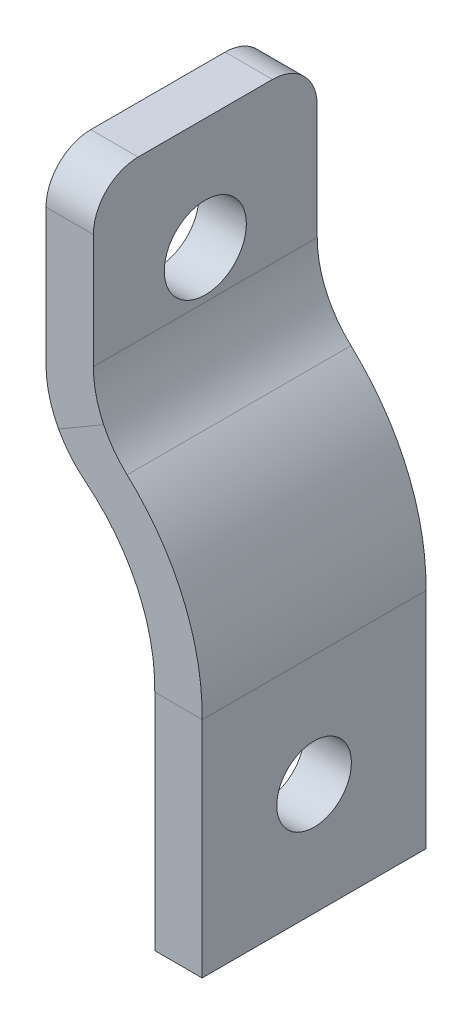
SolidWorks part; units mm, degrees
material "1060 Alloy"
ref_plane "Front Plane" through (0, 0, 0) normal (0, 0, 1) x (1, 0, 0)
ref_plane "Top Plane" through (0, 0, 0) normal (0, 1, 0) x (1, 0, 0)
ref_plane "Right Plane" through (0, 0, 0) normal (1, 0, 0) x (0, 0, -1)
sketch "Sketch1" plane through (0, 0, 0) normal (0, 0, 1) x (1, 0, 0)
  line L0 (-14.2875, 7.5) -> (-14.2875, -7.5)
  line L1 (-7, -20) -> (-7, -35)
  circle A0 centre (0, 0) radius 12.7 construction
  arc A1 (-14.2875, -7.5) -> (-7, -20) centre (-20.9984, -19.7867) cw
  point P3 (-12.7, 0)
  point P4 (0, -12.7)
  dimension "D1" = 25.4
  dimension "D6" = 14
  dimension "D2" = 15
  dimension "D3" = 15
  dimension "D4" = 7
  dimension "D5" = 1.5875
  dimension "D7" = 20
  dimension "D8" = 7.5
sketch "Sketch2" plane through (0, 0, 0) normal (0, 1, 0) x (1, 0, 0)
  line L0 (-14.2875, 0) -> (-6.9984, 0) construction
  line L1 (-12.7, -7.5) -> (-15.875, -7.5)
  line L2 (-12.7, -7.5) -> (-12.7, 7.5)
  line L3 (-12.7, 7.5) -> (-15.875, 7.5)
  line L4 (-15.875, -7.5) -> (-15.875, 7.5)
  line L5 (-12.7, -7.5) -> (-15.875, 7.5) construction
  line L6 (-12.7, 7.5) -> (-15.875, -7.5) construction
  point P0 (-14.2875, 0)
  dimension "D1" = 15
  dimension "D2" = 3.175
sweep "Sweep1" add profiles "Sketch2" path "Sketch1"
fillet "Fillet1" radius 7 2 edges at (-15.875, -8.4418, 0) (-12.7, -6.5918, 0)
sketch "Sketch3" plane through (-8.5875, 0, 0) normal (-1, 0, 0) x (0, 0, 1)
  line L0 (0, -20) -> (0, -35) construction
  circle A0 centre (0, -27.5) radius 2.5
  dimension "D1" = 5
hole_wizard "M5 Clearance Hole1" positions "Sketch4" profile "Sketch5" hole size "M5" standard "AS" end condition through all
sketch "Sketch4" plane through (-15.875, 0, 0) normal (-1, 0, 0) x (0, 0, 1)
  point P0 (0, 0)
sketch "Sketch5" plane through (-15.875, 0, 0) normal (0, 1, 0) x (0, 0, 1)
  line L0 (0, 0) -> (0, 10.4641)
  line L1 (0, 10.4641) -> (2.75, 10.4641)
  line L2 (2.75, 10.4641) -> (2.75, 0)
  line L5 (2.75, 0) -> (0, 0)
  line L11 (0, -6.35) -> (0, 107.95) construction
  dimension "Thru Hole Dia." = 5.5
  dimension "Thru Hole Depth" = 10.4641
extrude "Cut-Extrude1" cut sketch "Sketch3" against normal through all both and the other way through all
fillet "Fillet2" radius 3 2 edges at (-14.2875, 7.5, 7.5) (-14.2875, 7.5, -7.5)
equation "\"keelOutDiameter\"= 1in"
equation "\"keelInDiameter\"= \"keelOutDiameter\" - 0.125in"
equation "\"frontBoltClearance\"= 7.25mm"
equation "\"betweenBoltsDistance\"= 20mm"
equation "\"wingLength\"= 1.4m"
equation "\"frontTubeLength\"= \"wingLength\" / sin ( 34.95deg )"
equation "\"plateThickness\"= 5mm"
equation "\"crossBarOutDiameter\"= 1in"
equation "\"crossBarInDiameter\"= \"crossBarOutDiameter\" - 0.125in"
equation "\"frontToCrossBar\"= 466mm"
equation "\"cablePinDiameter\"= 5mm"
equation "\"D2@Sketch1\"=\"cablePinDiameter\"*3"
equation "\"D1@Sketch2\"=\"cablePinDiameter\"*3"
equation "\"D1@Sketch3\"=\"cablePinDiameter\""
